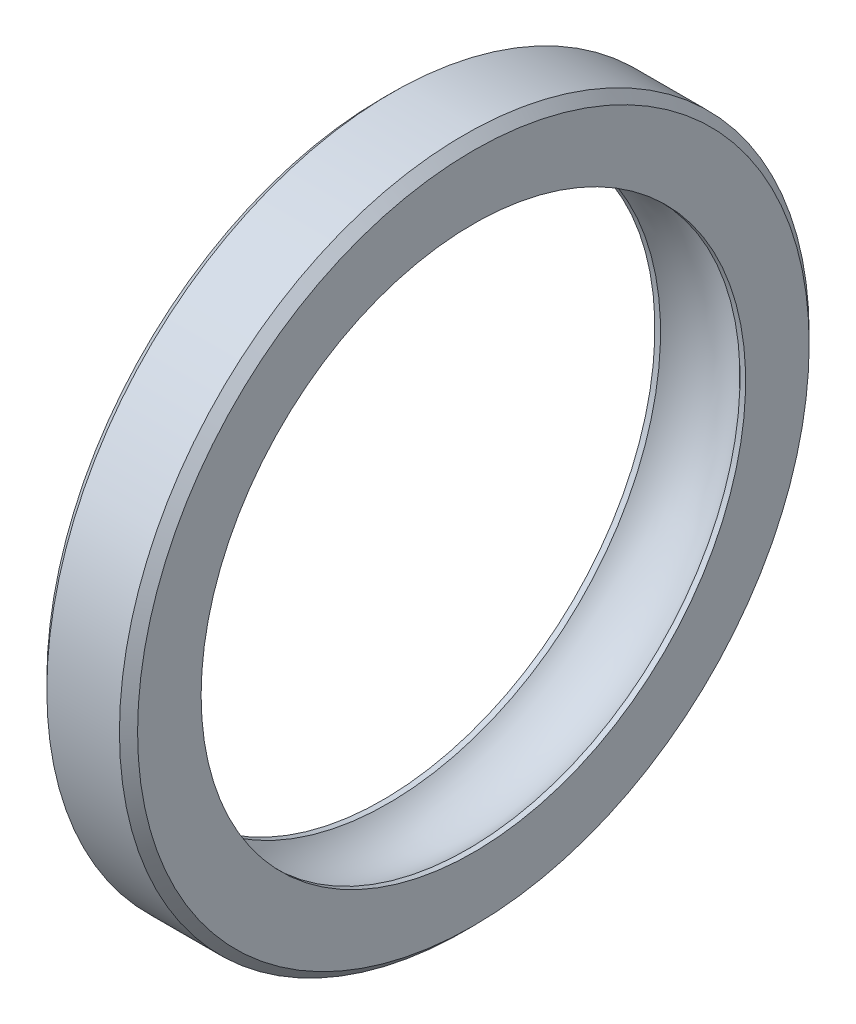
SolidWorks part; units mm, degrees
ref_plane "Front Plane" through (0, 0, 0) normal (0, 0, 1) x (1, 0, 0)
ref_plane "Top Plane" through (0, 0, 0) normal (0, 1, 0) x (1, 0, 0)
ref_plane "Right Plane" through (0, 0, 0) normal (1, 0, 0) x (0, 0, -1)
sketch "Sketch1" plane through (0, 0, 0) normal (0, 0, 1) x (1, 0, 0)
  line L0 (-21.3951, 0) -> (21.3951, 0) construction
  line L1 (0, -19.6409) -> (0, 19.6409) construction
  line L2 (-2.5, 15) -> (-2.1885, 15)
  line L3 (-2.5, 19) -> (2.5, 19)
  line L4 (-2.5, 19) -> (-2.5, 15)
  line L5 (2.1885, 15) -> (2.5, 15)
  line L6 (2.5, 19) -> (2.5, 15)
  line L7 (-2.5, 19) -> (2.5, 15) construction
  line L8 (-2.5, 15) -> (2.5, 19) construction
  line L9 (0, 12.9481) -> (0, 15)
  arc A0 (-2.1885, 15) -> (2.1885, 15) centre (0, 12.9481) cw
  point P0 (0, 17)
  point P4 (0, 0)
  point P7 (0, 0)
  dimension "D4" = 3
  dimension "D1" = 19
  dimension "D3" = 5
revolve "Revolve2" add sketch "Sketch1" angle 360 about L0
chamfer "Chamfer2" distance 0.5 angle 45 2 edges at (-2.5, 0, 19) (2.5, 0, 19)
